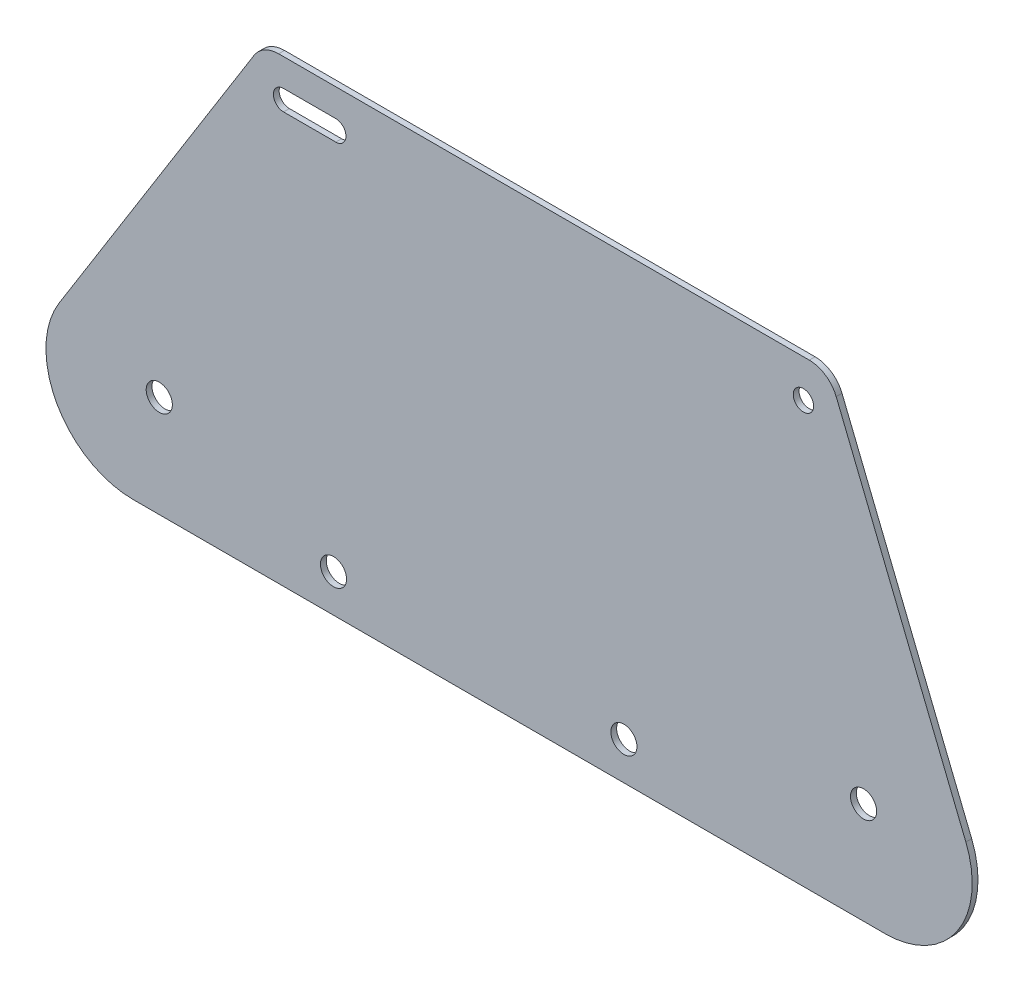
SolidWorks part; units mm, degrees
ref_plane "Front Plane" through (0, 0, 0) normal (0, 0, 1) x (1, 0, 0)
ref_plane "Top Plane" through (0, 0, 0) normal (0, 1, 0) x (1, 0, 0)
ref_plane "Right Plane" through (0, 0, 0) normal (1, 0, 0) x (0, 0, -1)
sketch "Sketch1" plane through (0, 0, 0) normal (0, 0, 1) x (1, 0, 0)
  line L0 (0, 0) -> (98.7294, 158)
  line L1 (0, 0) -> (357.5655, 0)
  line L3 (98.7294, 158) -> (293.7294, 158)
  line L5 (357.5655, 0) -> (293.7294, 158)
  line L6 (105.9354, 145) -> (123.9354, 145) construction
  line L7 (105.9354, 148.5) -> (123.9354, 148.5)
  line L8 (105.9354, 141.5) -> (123.9354, 141.5)
  arc A0 (105.9354, 148.5) -> (105.9354, 141.5) centre (105.9354, 145) ccw
  arc A1 (123.9354, 141.5) -> (123.9354, 148.5) centre (123.9354, 145) ccw
  circle A2 centre (284.9607, 145) radius 3.5
  circle A3 centre (305.6759, 35) radius 4.5
  circle A4 centre (63.1417, 35) radius 4.5
  circle A5 centre (123.1417, 13) radius 4.5
  circle A6 centre (223.1417, 13) radius 4.5
  point P1 (114.9354, 145)
  dimension "D9" = 7
  dimension "D15" = 9
  dimension "D16" = 9
  dimension "D17" = 9
  dimension "D1" = 158
  dimension "D2" = 195
  dimension "D3" = 68
  dimension "D4" = 58
  dimension "D5" = 7
  dimension "D6" = 13
  dimension "D7" = 13
  dimension "D8" = 18
  dimension "D10" = 13
  dimension "D11" = 13
  dimension "D12" = 35
  dimension "D13" = 35
  dimension "D14" = 35
  dimension "D18" = 13
  dimension "D19" = 100
  dimension "D20" = 60
extrude "Boss-Extrude1" add sketch "Sketch1" along normal blind 2
fillet "Fillet1" radius 30 2 edges at (0, 0, 1) (357.5655, 0, 1)
fillet "Fillet2" radius 10 2 edges at (293.7294, 158, 1) (98.7294, 158, 1)
